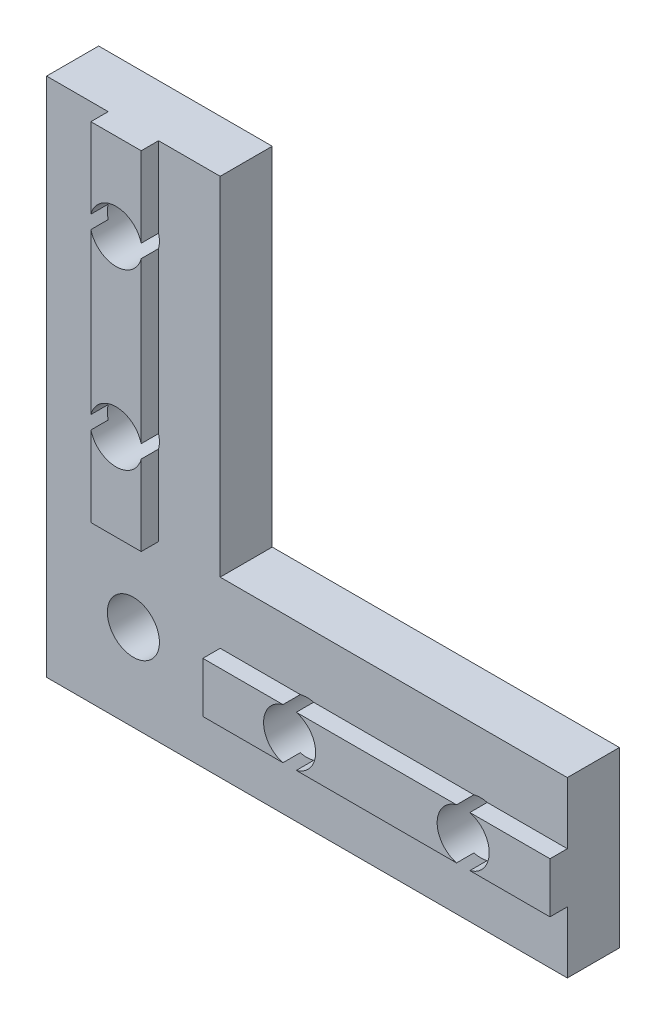
SolidWorks part; units mm, degrees
ref_plane "Front Plane" through (0, 0, 0) normal (0, 0, 1) x (1, 0, 0)
ref_plane "Top Plane" through (0, 0, 0) normal (0, 1, 0) x (1, 0, 0)
ref_plane "Right Plane" through (0, 0, 0) normal (1, 0, 0) x (0, 0, -1)
sketch "Esquisse1" plane through (0, 0, 0) normal (0, 0, 1) x (1, 0, 0)
  line L0 (0, 0) -> (30, 0)
  line L1 (30, 0) -> (30, 10)
  line L2 (30, 10) -> (10, 10)
  line L3 (10, 10) -> (10, 30)
  line L4 (10, 30) -> (0, 30)
  line L5 (0, 30) -> (0, 0)
  circle A0 centre (5, 25) radius 1.5
  circle A1 centre (5, 15) radius 1.5
  circle A2 centre (5, 5) radius 1.5
  circle A3 centre (15, 5) radius 1.5
  circle A4 centre (25, 5) radius 1.5
  point P18 (5, 30)
  point P20 (30, 5)
  dimension "D2" = 3
  dimension "D1" = 10
  dimension "D3" = 30
  dimension "D4" = 10
  dimension "D5" = 5
  dimension "D6" = 10
  dimension "D7" = 10
extrude "Boss.-Extru.1" add sketch "Esquisse1" along normal blind 3
sketch "Esquisse2" plane through (0, 0, 3) normal (0, 0, 1) x (1, 0, 0)
  line L0 (10, 30) -> (0, 30) construction
  line L1 (3.55, 30) -> (6.45, 30)
  line L2 (3.55, 30) -> (3.55, 10)
  line L3 (3.55, 10) -> (6.45, 10)
  line L4 (6.45, 30) -> (6.45, 10)
  line L5 (30, 10) -> (10, 10) construction
  line L6 (30, 0) -> (30, 10) construction
  line L7 (30, 6.45) -> (10, 6.45)
  line L8 (30, 6.45) -> (30, 3.55)
  line L9 (30, 3.55) -> (10, 3.55)
  line L10 (10, 6.45) -> (10, 3.55)
  line L11 (10, 10) -> (10, 30) construction
  point P4 (5, 30)
  point P7 (5, 30)
  point P18 (30, 5)
  point P19 (30, 5)
  dimension "D1" = 2.9
extrude "Boss.-Extru.2" add sketch "Esquisse2" along normal blind 1
sketch "Esquisse3" plane through (0, 0, 4) normal (0, 0, 1) x (1, 0, 0)
  circle A0 centre (5, 25) radius 1.5
  arc A1 (6.45, 25.3841) -> (3.55, 25.3841) centre (5, 25) ccw construction
  circle A2 centre (5, 15) radius 1.5
  circle A3 centre (15, 5) radius 1.5
  circle A4 centre (25, 5) radius 1.5
  arc A5 (25.3841, 3.55) -> (25.3841, 6.45) centre (25, 5) ccw construction
  arc A6 (15.3841, 3.55) -> (15.3841, 6.45) centre (15, 5) ccw construction
  circle A7 centre (5, 15) radius 1.5 construction
extrude "Enlèv. mat.-Extru.1" cut sketch "Esquisse3" against normal through all
